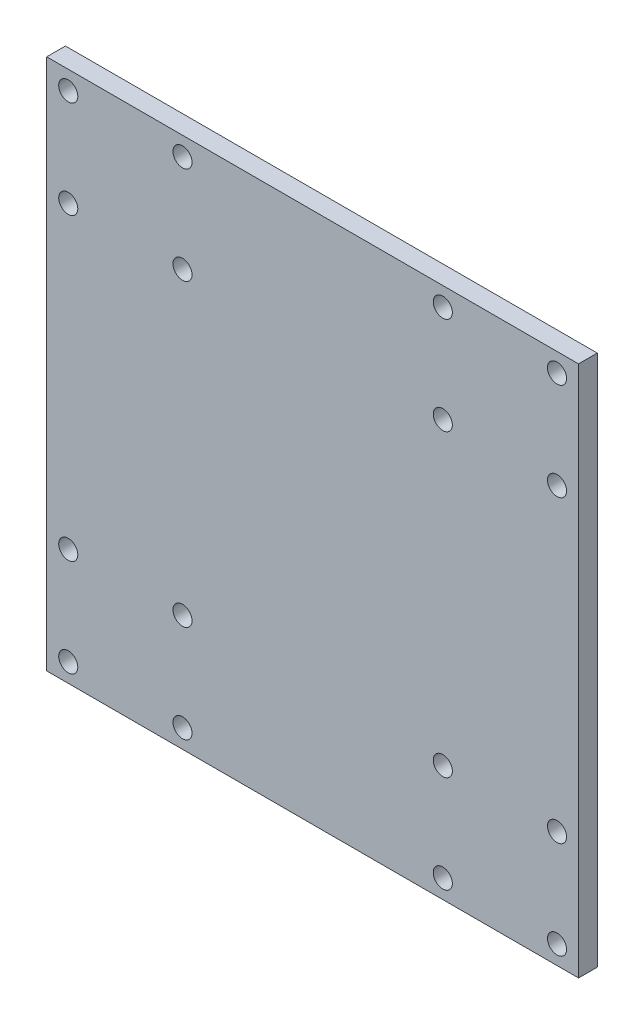
SolidWorks part; units mm, degrees
ref_plane "Front Plane" through (0, 0, 0) normal (0, 0, 1) x (1, 0, 0)
ref_plane "Top Plane" through (0, 0, 0) normal (0, 1, 0) x (1, 0, 0)
ref_plane "Right Plane" through (0, 0, 0) normal (1, 0, 0) x (0, 0, -1)
sketch "Sketch1" plane through (0, 0, 0) normal (0, 0, 1) x (1, 0, 0)
  line L1 (-71, -71) -> (71, -71)
  line L2 (-71, -71) -> (-71, 71)
  line L3 (-71, 71) -> (71, 71)
  line L4 (71, -71) -> (71, 71)
  line L5 (-71, -71) -> (71, 71) construction
  line L6 (-71, 71) -> (71, -71) construction
  point P0 (0, 0)
  dimension "D1" = 142
  dimension "D2" = 142
extrude "Boss-Extrude1" add sketch "Sketch1" along normal mid plane 5
sketch "Sketch2" plane through (0, 0, 2.5) normal (0, 0, 1) x (1, 0, 0)
  line L3 (-65.25, 71) -> (-65.25, -71)
  line L4 (-65.25, 71) -> (-65.25, -71) construction
  line L6 (65.25, -71) -> (65.25, 71)
  line L7 (65.25, -71) -> (65.25, 71) construction
  line L13 (-34.75, 71) -> (-34.75, -71)
  line L14 (-34.75, 71) -> (-34.75, -71) construction
  line L16 (34.75, -71) -> (34.75, 71)
  line L18 (34.75, -71) -> (34.75, 71) construction
  line L20 (71, 66) -> (-71, 66)
  line L21 (71, 66) -> (-71, 66) construction
  line L23 (-71, -66) -> (71, -66)
  line L24 (-71, -66) -> (71, -66) construction
  line L26 (71, 40) -> (-71, 40)
  line L27 (71, 40) -> (-71, 40) construction
  line L29 (-71, -40) -> (71, -40)
  line L30 (-71, -40) -> (71, -40) construction
  circle A0 centre (-65.25, 66) radius 2.55
  circle A1 centre (-34.75, 66) radius 2.55
  circle A2 centre (-34.75, 40) radius 2.55
  circle A3 centre (-65.25, 40) radius 2.55
  circle A4 centre (65.25, 66) radius 2.55
  circle A5 centre (65.25, 40) radius 2.55
  circle A6 centre (34.75, 40) radius 2.55
  circle A7 centre (34.75, 66) radius 2.55
  circle A8 centre (-65.25, -40) radius 2.55
  circle A9 centre (-34.75, -40) radius 2.55
  circle A10 centre (-34.75, -66) radius 2.55
  circle A11 centre (-65.25, -66) radius 2.55
  circle A12 centre (34.75, -40) radius 2.55
  circle A13 centre (65.25, -40) radius 2.55
  circle A14 centre (65.25, -66) radius 2.55
  circle A15 centre (34.75, -66) radius 2.55
  dimension "D9" = 5.1
  dimension "D10" = 5.1
  dimension "D11" = 5.1
  dimension "D12" = 5.1
  dimension "D13" = 5.1
  dimension "D14" = 5.1
  dimension "D15" = 5.1
  dimension "D16" = 5.1
  dimension "D17" = 5.1
  dimension "D18" = 5.1
  dimension "D19" = 5.1
  dimension "D20" = 5.1
  dimension "D21" = 5.1
  dimension "D22" = 5.1
  dimension "D23" = 5.1
  dimension "D24" = 5.1
  dimension "D1" = 5.75
  dimension "D2" = 5.75
  dimension "D3" = 36.25
  dimension "D4" = 36.25
  dimension "D5" = 5
  dimension "D6" = 5
  dimension "D7" = 31
  dimension "D8" = 31
extrude "Cut-Extrude1" cut sketch "Sketch2" against normal through all
